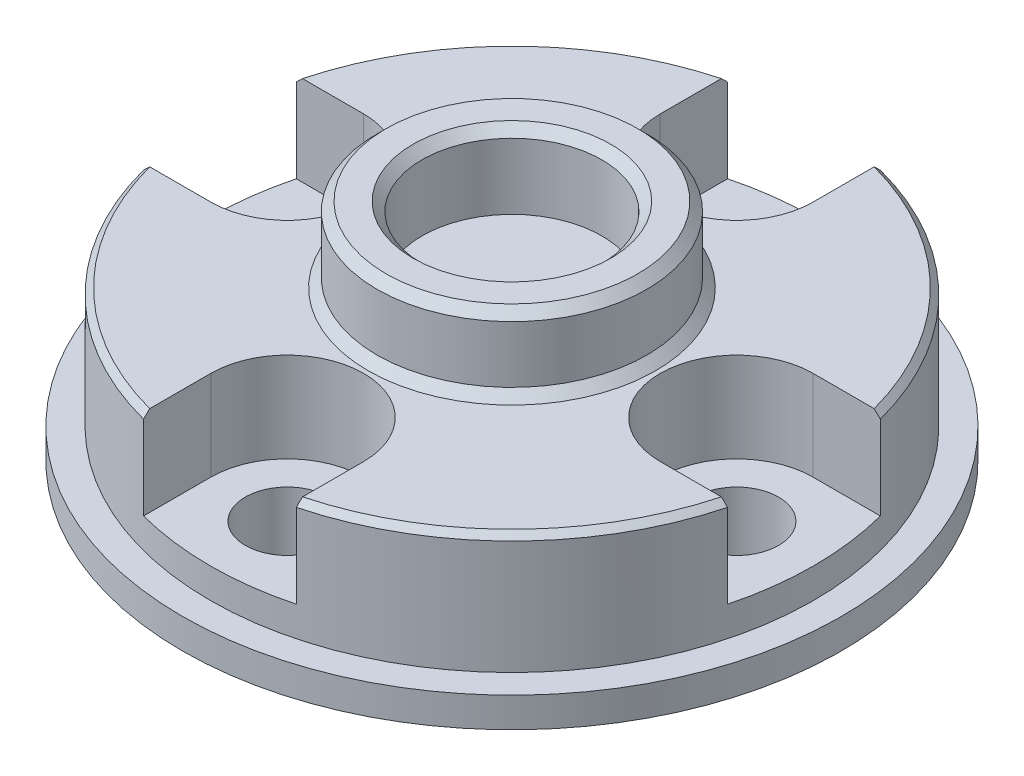
SolidWorks part; units mm, degrees
ref_plane "Front Plane" through (0, 0, 0) normal (0, 0, 1) x (1, 0, 0)
ref_plane "Top Plane" through (0, 0, 0) normal (0, 1, 0) x (1, 0, 0)
ref_plane "Right Plane" through (0, 0, 0) normal (1, 0, 0) x (0, 0, -1)
sketch "Sketch1" plane through (0, 0, 0) normal (0, 1, 0) x (1, 0, 0)
  circle A0 centre (0, 0) radius 11
  dimension "D1" = 22
extrude "Boss-Extrude1" add sketch "Sketch1" along normal blind 1
sketch "Sketch2" plane through (0, 1, 0) normal (0, 1, 0) x (1, 0, 0)
  circle A0 centre (0, 0) radius 10.075
  dimension "D1" = 20.15
extrude "Boss-Extrude2" add sketch "Sketch2" along normal blind 4
chamfer "Chamfer1" distance 0.2 angle 45 1 edges at (0, 5, 10.075)
sketch "Sketch3" plane through (0, 5, 0) normal (0, 1, 0) x (1, 0, 0)
  circle A0 centre (0, 7.5) radius 1.4
  circle A1 centre (7.5, 0) radius 1.4
  circle A2 centre (0, -7.5) radius 1.4
  circle A3 centre (-7.5, 0) radius 1.4
  point P12 (0, 0)
  dimension "D1" = 2.8
  dimension "D2" = 7.5
extrude "Cut-Extrude1" cut sketch "Sketch3" against normal through all
sketch "Sketch4" plane through (0, 5, 0) normal (0, 1, 0) x (1, 0, 0)
  line L0 (-2.55, 7.5) -> (-2.55, 9.747)
  line L1 (2.55, 7.5) -> (2.55, 9.747)
  line L2 (7.5, -2.55) -> (9.747, -2.55)
  line L3 (7.5, 2.55) -> (9.747, 2.55)
  line L4 (-2.55, -7.5) -> (-2.55, -9.747)
  line L5 (2.55, -7.5) -> (2.55, -9.747)
  line L6 (-7.5, 2.55) -> (-9.747, 2.55)
  line L7 (-7.5, -2.55) -> (-9.747, -2.55)
  arc A0 (-2.55, 7.5) -> (2.55, 7.5) centre (0, 7.5) ccw
  circle A1 centre (0, 0) radius 10.075 construction
  circle A2 centre (0, 0) radius 10.075 construction
  arc A3 (-2.55, 9.747) -> (2.55, 9.747) centre (0, 0) cw
  arc A4 (7.5, 2.55) -> (7.5, -2.55) centre (7.5, 0) ccw
  arc A5 (9.747, 2.55) -> (9.747, -2.55) centre (0, 0) cw
  arc A6 (2.55, -7.5) -> (-2.55, -7.5) centre (0, -7.5) ccw
  arc A7 (2.55, -9.747) -> (-2.55, -9.747) centre (0, 0) cw
  arc A8 (-7.5, -2.55) -> (-7.5, 2.55) centre (-7.5, 0) ccw
  arc A9 (-9.747, -2.55) -> (-9.747, 2.55) centre (0, 0) cw
  point P29 (0, 0)
  dimension "D1" = 5.1
extrude "Cut-Extrude2" cut sketch "Sketch4" against normal offset from surface (3 mm away) 2 up to face at (0, 0, -6.1)
sketch "Sketch5" plane through (0, 5, 0) normal (0, 1, 0) x (1, 0, 0)
  circle A0 centre (0, 0) radius 4.5
  dimension "D1" = 9
extrude "Boss-Extrude3" add sketch "Sketch5" along normal blind 2.5 contours A0
sketch "Sketch6" plane through (0, 7.5, 0) normal (0, 1, 0) x (1, 0, 0)
  circle A0 centre (0, 0) radius 3
  dimension "D1" = 6
extrude "Cut-Extrude3" cut sketch "Sketch6" against normal blind 2.5
chamfer "Chamfer2" distance 0.3 angle 45 3 edges at (0, 5, 4.5) (0, 7.5, 3) (0, 7.5, 4.5)
